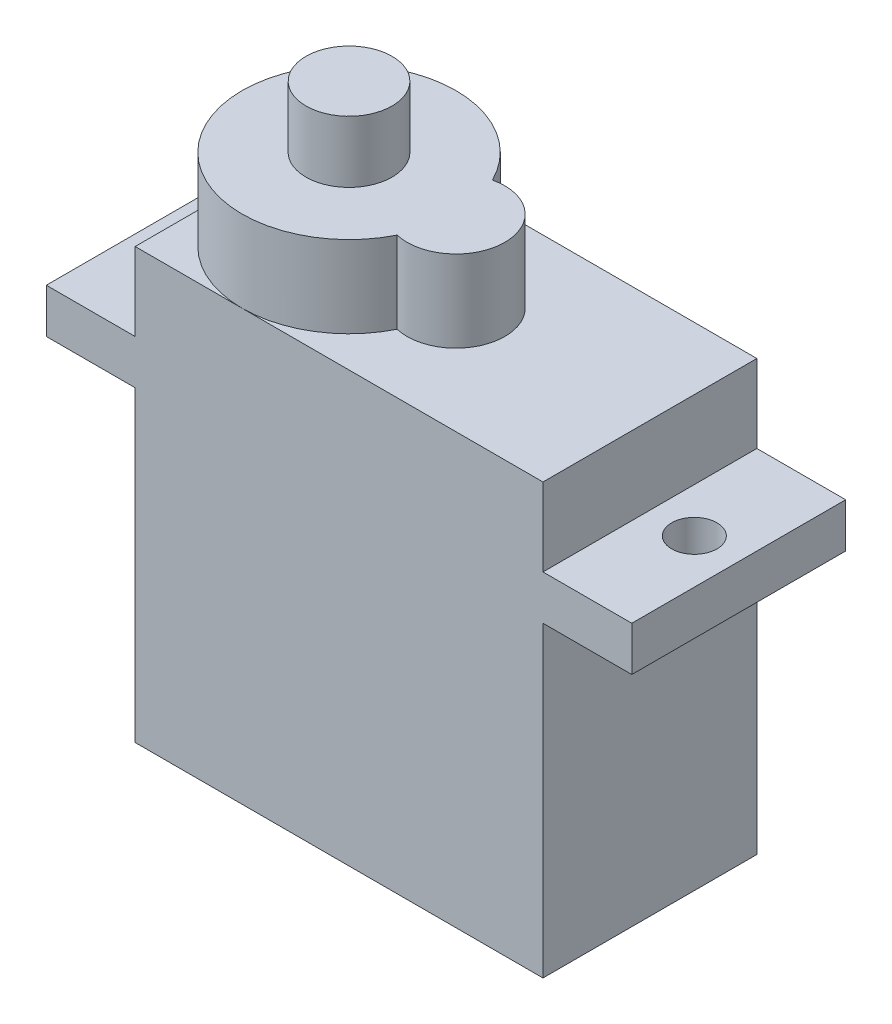
SolidWorks part; units mm, degrees
ref_plane "Front Plane" through (0, 0, 0) normal (0, 0, 1) x (1, 0, 0)
ref_plane "Top Plane" through (0, 0, 0) normal (0, 1, 0) x (1, 0, 0)
ref_plane "Right Plane" through (0, 0, 0) normal (1, 0, 0) x (0, 0, -1)
sketch "Sketch1" plane through (0, 0, 0) normal (0, 0, 1) x (1, 0, 0)
  line L0 (0, 23.7) -> (0, 19.4) construction
  line L1 (0, 0) -> (22.5, 0)
  line L2 (0, 0) -> (0, 16.95)
  line L3 (0, 23.7) -> (22.5, 23.7)
  line L4 (22.5, 0) -> (22.5, 16.95)
  line L6 (0, 16.95) -> (-4.9, 16.95)
  line L7 (-4.9, 16.95) -> (-4.9, 19.4)
  line L8 (-4.9, 19.4) -> (0, 19.4)
  line L9 (0, 19.4) -> (0, 23.7)
  line L10 (22.5, 19.4) -> (27.4, 19.4)
  line L11 (27.4, 19.4) -> (27.4, 16.95)
  line L12 (27.4, 16.95) -> (22.5, 16.95)
  line L13 (22.5, 19.4) -> (22.5, 23.7)
  dimension "D1" = 4.9
  dimension "D2" = 22.5
  dimension "D3" = 23.7
  dimension "D4" = 4.3
  dimension "D5" = 4.3
  dimension "D6" = 2.45
  dimension "D7" = 2.45
  dimension "D8" = 4.9
extrude "Boss-Extrude1" add sketch "Sketch1" along normal blind 11.8
sketch "Sketch2" plane through (0, 23.7, 0) normal (0, 1, 0) x (1, 0, 0)
  line L0 (14.5, -5.9) -> (22.5, -5.9) construction
  line L1 (22.5, -11.8) -> (22.5, 0) construction
  arc A1 (11.1822, -3.2716) -> (11.1822, -8.5284) centre (5.9, -5.9) ccw
  arc A2 (11.1822, -8.5284) -> (11.1822, -3.2716) centre (11.8, -5.9) ccw
extrude "Boss-Extrude2" add sketch "Sketch2" along normal blind 4.5
sketch "Sketch3" plane through (0, 28.2, 0) normal (0, 1, 0) x (1, 0, 0)
  circle A0 centre (5.9, -5.9) radius 2.375
  dimension "D1" = 4.75
extrude "Boss-Extrude3" add sketch "Sketch3" along normal blind 3.4
sketch "Sketch4" plane through (0, 19.4, 0) normal (0, 1, 0) x (1, 0, 0)
  line L0 (-4.9, -5.9) -> (0, -5.9) construction
  line L1 (-4.9, -11.8) -> (-4.9, 0) construction
  line L2 (22.5, -5.9) -> (27.4, -5.9) construction
  line L3 (22.5, -11.8) -> (22.5, 0) construction
  line L4 (27.4, -11.8) -> (27.4, 0) construction
  arc A0 (11.1822, -3.2716) -> (11.1822, -8.5284) centre (5.9, -5.9) ccw construction
  circle A1 centre (-2.45, -5.9) radius 1.25
  circle A2 centre (24.95, -5.9) radius 1.25
extrude "Cut-Extrude1" cut sketch "Sketch4" against normal up to next
